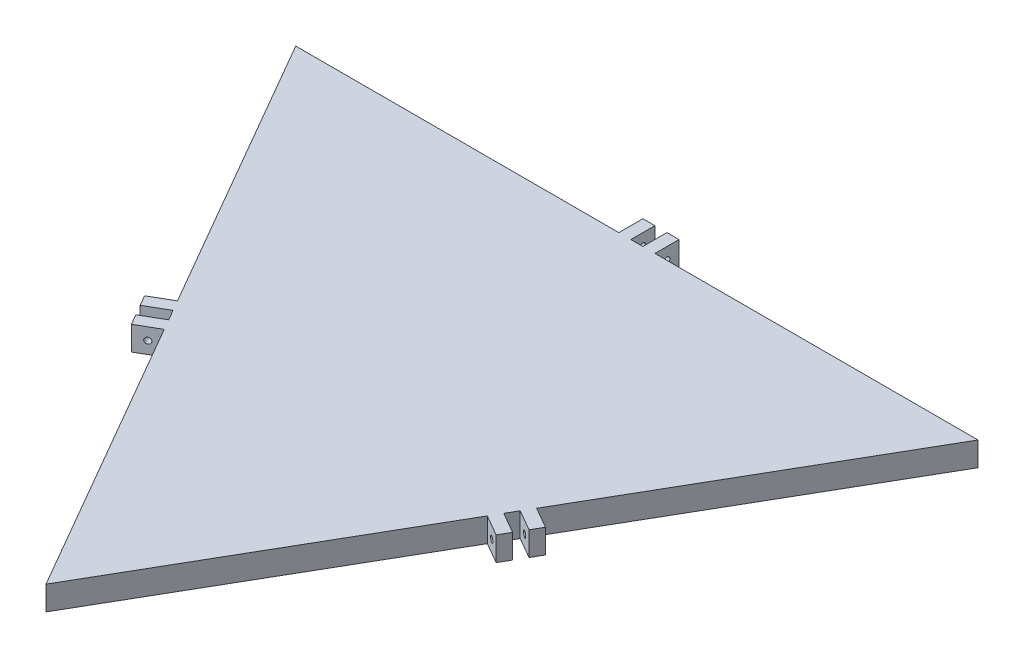
SolidWorks part; units mm, degrees
material "Plain Carbon Steel"
ref_plane "Front Plane" through (0, 0, 0) normal (0, 0, 1) x (1, 0, 0)
ref_plane "Top Plane" through (0, 0, 0) normal (0, 1, 0) x (1, 0, 0)
ref_plane "Right Plane" through (0, 0, 0) normal (1, 0, 0) x (0, 0, -1)
sketch "Sketch2" plane through (0, 0, 0) normal (0, 1, 0) x (1, 0, 0)
  line L0 (-283.5, 163.6788) -> (283.5, 163.6788)
  line L1 (0, -327.3576) -> (283.5, 163.6788)
  line L2 (0, -327.3576) -> (-283.5, 163.6788)
  circle A0 centre (0, 0) radius 163.6788
  point P23 (0, 0)
  dimension "D4" = 567
extrude "Boss-Extrude1" add sketch "Sketch2" along normal blind 20 contours L2 L1 L0 A0 | A0
sketch "Sketch3" plane through (141.75, 0, 81.8394) normal (0.866, 0, 0.5) x (0.5, 0, -0.866)
  line L1 (-5, 20) -> (-15, 20)
  line L2 (-5, 20) -> (-5, 0)
  line L3 (-5, 0) -> (-15, 0)
  line L4 (-15, 20) -> (-15, 0)
  line L6 (0, 20) -> (0, 0) construction
  line L7 (5, 20) -> (15, 20)
  line L8 (5, 20) -> (5, 0)
  line L9 (5, 0) -> (15, 0)
  line L10 (15, 20) -> (15, 0)
  line L11 (-283.5, 20) -> (283.5, 20) construction
  line L12 (-283.5, 0) -> (283.5, 0) construction
  dimension "D1" = 10
  dimension "D2" = 5
  dimension "D3" = 5
extrude "Boss-Extrude2" add sketch "Sketch3" along normal blind 20
ref_plane "Plane1" through (0, 0, 0) normal (1, 0, 0) x (0, 0, -1)
ref_plane "Plane2" through (0, 0, 0) normal (0.5, 0, 0.866) x (0.866, 0, -0.5)
sketch "Sketch4" plane through (-7.5, 0, 12.9904) normal (-0.5, 0, 0.866) x (0.866, 0, 0.5)
  line L0 (183.6788, 20) -> (163.6788, 20) construction
  line L1 (183.6788, 20) -> (183.6788, 0) construction
  circle A0 centre (173.6788, 10) radius 2.5
  point P4 (173.6788, 20)
  point P7 (183.6788, 10)
  dimension "D1" = 5
extrude "Cut-Extrude1" cut sketch "Sketch4" against normal up to surface (30 mm away) up to face at (157.9103, 10, 73.849)
mirror "Mirror1" about plane through (0, 0, 0) normal (0.5, 0, 0.866) of "Cut-Extrude1", "Boss-Extrude2" second plane through (0, 0, 0) second plane normal (1, 0, 0)
equation "\"D3@Sketch3\"=\"D2@Sketch3\""
